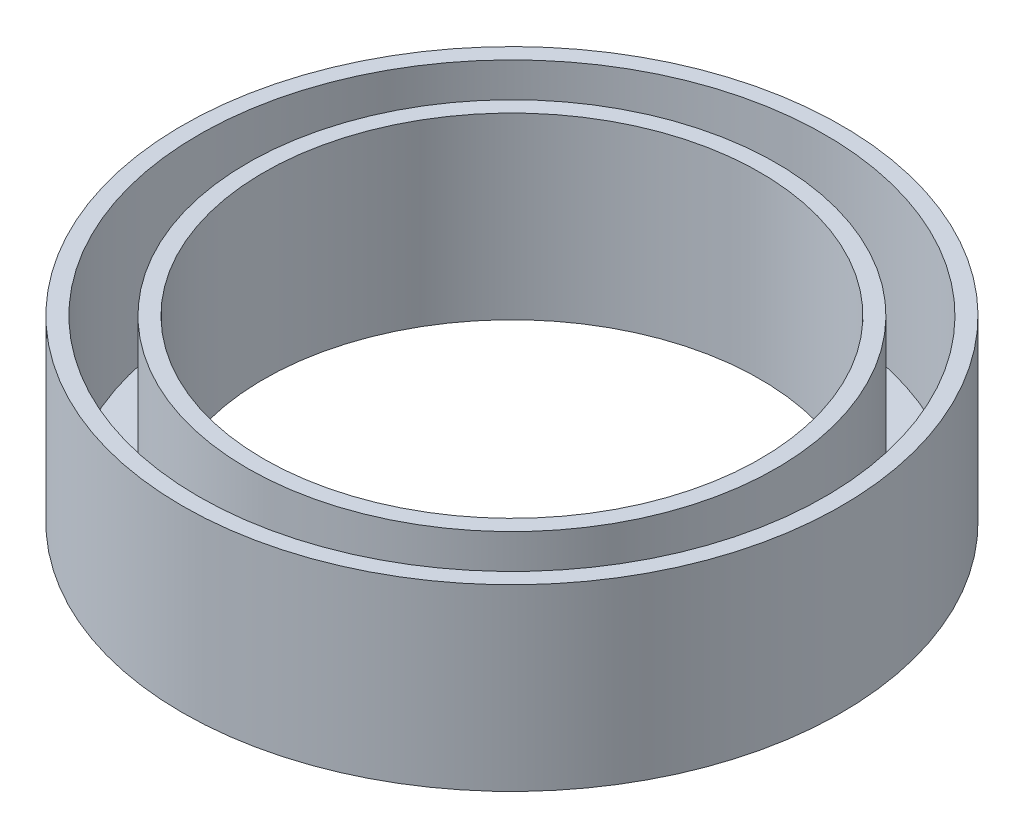
SolidWorks part; units mm, degrees
ref_plane "前视基准面" through (0, 0, 0) normal (0, 0, 1) x (1, 0, 0)
ref_plane "上视基准面" through (0, 0, 0) normal (0, 1, 0) x (1, 0, 0)
ref_plane "右视基准面" through (0, 0, 0) normal (1, 0, 0) x (0, 0, -1)
other "Configuration Table"
sketch "草图1" plane through (0, 0, 0) normal (0, 1, 0) x (1, 0, 0)
  circle A0 centre (0, 0) radius 16.25
  circle A2 centre (0, 0) radius 19.25
  dimension "D1" = 32.5
  dimension "D2" = 3
extrude "凸台-拉伸1" add sketch "草图1" along normal blind 1
sketch "草图3" plane through (0, 1, 0) normal (0, 1, 0) x (1, 0, 0)
  circle A0 centre (0, 0) radius 16.25 construction
  circle A1 centre (0, 0) radius 16.25
  circle A2 centre (0, 0) radius 15.25
  circle A4 centre (0, 0) radius 19.25 construction
  circle A5 centre (0, 0) radius 20.25
  circle A6 centre (0, 0) radius 20.25
  circle A7 centre (0, 0) radius 19.25
  circle M5 centre (0, 0) radius 19.25
  circle M6 centre (0, 0) radius 16.25
  dimension "D1" = 1
  dimension "D2" = 1
extrude "凸台-拉伸3" add sketch "草图3" along normal blind 10 and the other way blind 1 contours A6 M5 | A2 M6
